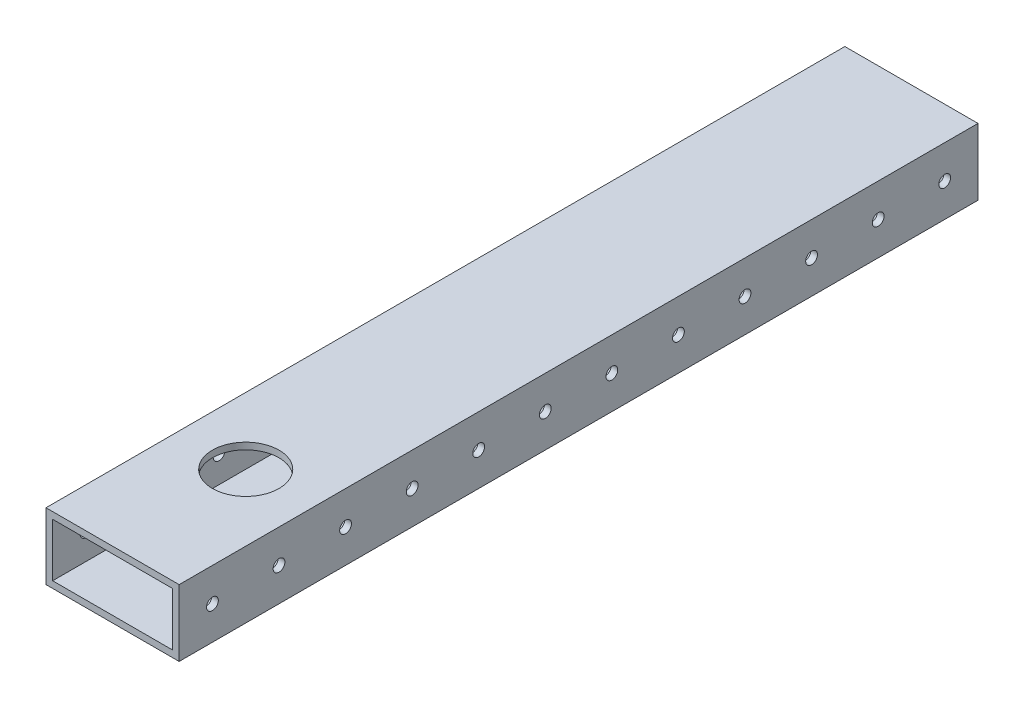
SolidWorks part; units mm, degrees
ref_plane "Front Plane" through (0, 0, 0) normal (0, 0, 1) x (1, 0, 0)
ref_plane "Top Plane" through (0, 0, 0) normal (0, 1, 0) x (1, 0, 0)
ref_plane "Right Plane" through (0, 0, 0) normal (1, 0, 0) x (0, 0, -1)
sketch "Sketch1" plane through (0, 0, 0) normal (0, 0, 1) x (1, 0, 0)
  line L1 (-25.4, -12.7) -> (25.4, -12.7)
  line L2 (-25.4, -12.7) -> (-25.4, 12.7)
  line L3 (-25.4, 12.7) -> (25.4, 12.7)
  line L4 (25.4, -12.7) -> (25.4, 12.7)
  line L5 (-25.4, -12.7) -> (25.4, 12.7) construction
  line L6 (-25.4, 12.7) -> (25.4, -12.7) construction
  line L7 (-22.86, -10.16) -> (22.86, -10.16)
  line L8 (-22.86, -10.16) -> (-22.86, 10.16)
  line L9 (-22.86, 10.16) -> (22.86, 10.16)
  line L10 (22.86, -10.16) -> (22.86, 10.16)
  line L11 (-22.86, -10.16) -> (22.86, 10.16) construction
  line L12 (-22.86, 10.16) -> (22.86, -10.16) construction
  point P0 (0, 0)
  point P6 (0, 0)
  dimension "D1" = 50.8
  dimension "D2" = 25.4
  dimension "D3" = 2.54
  dimension "D4" = 2.54
extrude "Boss-Extrude1" add sketch "Sketch1" against normal blind 355.6
hole_wizard "#8 Clearance Hole1" positions "Sketch2" profile "Sketch3" hole size "#8" standard "ANSI Inch" end condition through all
sketch "Sketch2" plane through (25.4, 0, 0) normal (1, 0, 0) x (0, 0, -1)
  line L0 (355.6, -12.7) -> (0, -12.7) construction
  point P0 (12.7, 0)
  point P16 (38.1, 0)
  point P17 (63.5, 0)
  point P18 (88.9, 0)
  point P19 (114.3, 0)
  point P20 (139.7, 0)
  point P21 (165.1, 0)
  point P22 (190.5, 0)
  point P23 (215.9, 0)
  point P24 (241.3, 0)
  point P25 (266.7, 0)
  point P26 (292.1, 0)
  point P27 (317.5, 0)
  point P28 (342.9, 0)
  dimension "D1" = 12.7
  dimension "D2" = 12.7
  dimension "D3" = 14
sketch "Sketch3" plane through (25.4, 0, -12.7) normal (0, 1, 0) x (0, 0, -1)
  line L0 (0, 0) -> (0, 50.8)
  line L1 (0, 50.8) -> (2.2479, 50.8)
  line L2 (2.2479, 50.8) -> (2.2479, 0)
  line L5 (2.2479, 0) -> (0, 0)
  line L11 (0, -6.35) -> (0, 107.95) construction
  dimension "Thru Hole Dia." = 4.4958
  dimension "Thru Hole Depth" = 50.8
hole_wizard "1 (1) Diameter Hole1" positions "Sketch6" profile "Sketch7" hole size "1" standard "ANSI Inch" end condition through all
sketch "Sketch6" plane through (0, 12.7, 0) normal (0, 1, 0) x (1, 0, 0)
  line L0 (25.4, 355.6) -> (25.4, 0) construction
  line L1 (25.4, 0) -> (-25.4, 0) construction
  point P0 (0, 101.6)
  dimension "D1" = 25.4
  dimension "D2" = 101.6
sketch "Sketch7" plane through (0, 12.7, -101.6) normal (1, 0, 0) x (0, 0, 1)
  line L0 (0, 0) -> (0, 25.4)
  line L1 (0, 25.4) -> (12.7, 25.4)
  line L2 (12.7, 25.4) -> (12.7, 0)
  line L5 (12.7, 0) -> (0, 0)
  line L11 (0, -6.35) -> (0, 107.95) construction
  dimension "Thru Hole Dia." = 25.4
  dimension "Thru Hole Depth" = 25.4
sketch "Sketch8" plane through (0, 12.7, 0) normal (0, 1, 0) x (1, 0, 0)
  line L0 (25.4, 0) -> (25.4, 50.8)
  line L1 (25.4, 355.6) -> (25.4, 0) construction
  line L2 (25.4, 50.8) -> (60.3179, 50.8)
  line L3 (60.3179, 50.8) -> (60.3179, -5.2193)
  line L4 (60.3179, -5.2193) -> (-35.9606, -5.2193)
  line L5 (-35.9606, -5.2193) -> (-35.9606, 50.8)
  line L6 (-35.9606, 50.8) -> (25.4, 50.8)
  line M3 (-25.4, 0) -> (25.4, 0)
  line M4 (25.4, 0) -> (25.4, 355.6)
  line M6 (-25.4, 355.6) -> (-25.4, 0)
  dimension "D1" = 50.8
extrude "Cut-Extrude1" cut sketch "Sketch8" against normal blind 71.882 and the other way blind 421.64 contours L6 M6 M3 M4
